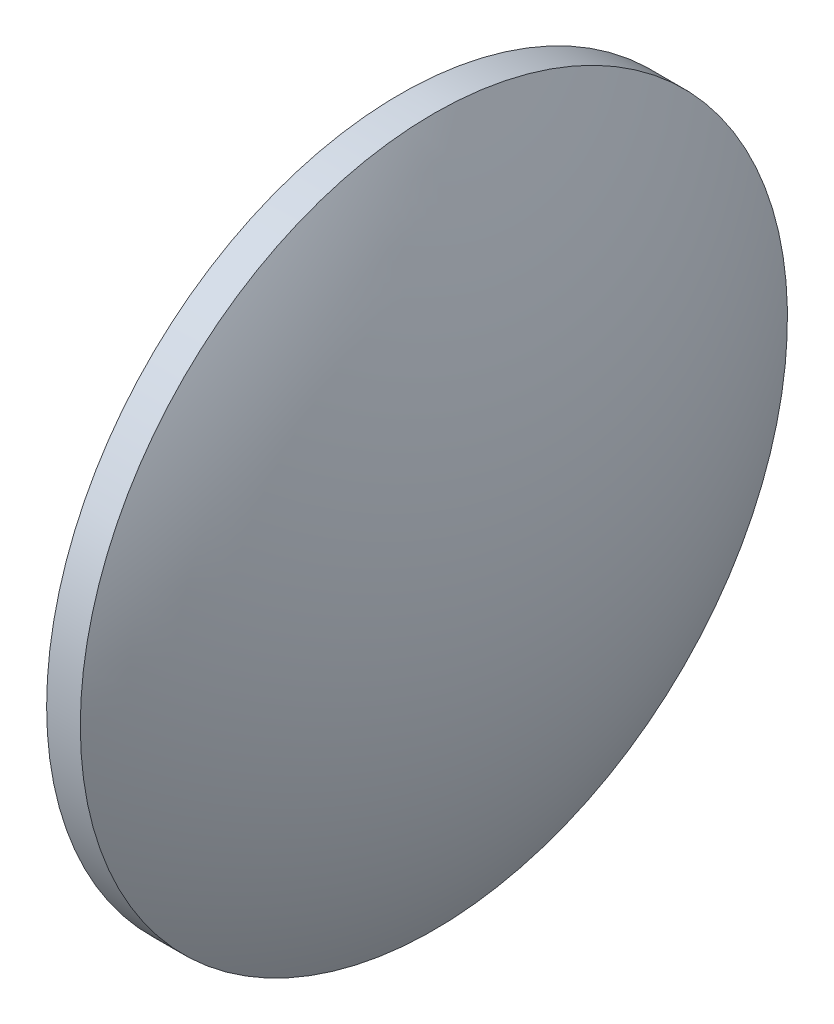
SolidWorks part; units mm, degrees
ref_plane "前视基准面" through (0, 0, 0) normal (0, 0, 1) x (1, 0, 0)
ref_plane "上视基准面" through (0, 0, 0) normal (0, 1, 0) x (1, 0, 0)
ref_plane "右视基准面" through (0, 0, 0) normal (1, 0, 0) x (0, 0, -1)
sketch "草图1" plane through (0, 0, 0) normal (0, 0, 1) x (1, 0, 0)
  line L0 (218.1237, 130.5186) -> (262.0758, 130.5186) construction
  line L1 (226.8933, 130.5186) -> (226.8933, 162.0186)
  line L2 (226.8933, 162.0186) -> (229.8933, 162.0186)
  line L3 (238.1033, 130.5186) -> (226.8933, 130.5186)
  arc A0 (238.1033, 130.5186) -> (229.8933, 162.0186) centre (173.5689, 130.5186) ccw
revolve "旋转1" add sketch "草图1" angle 360 about L0
